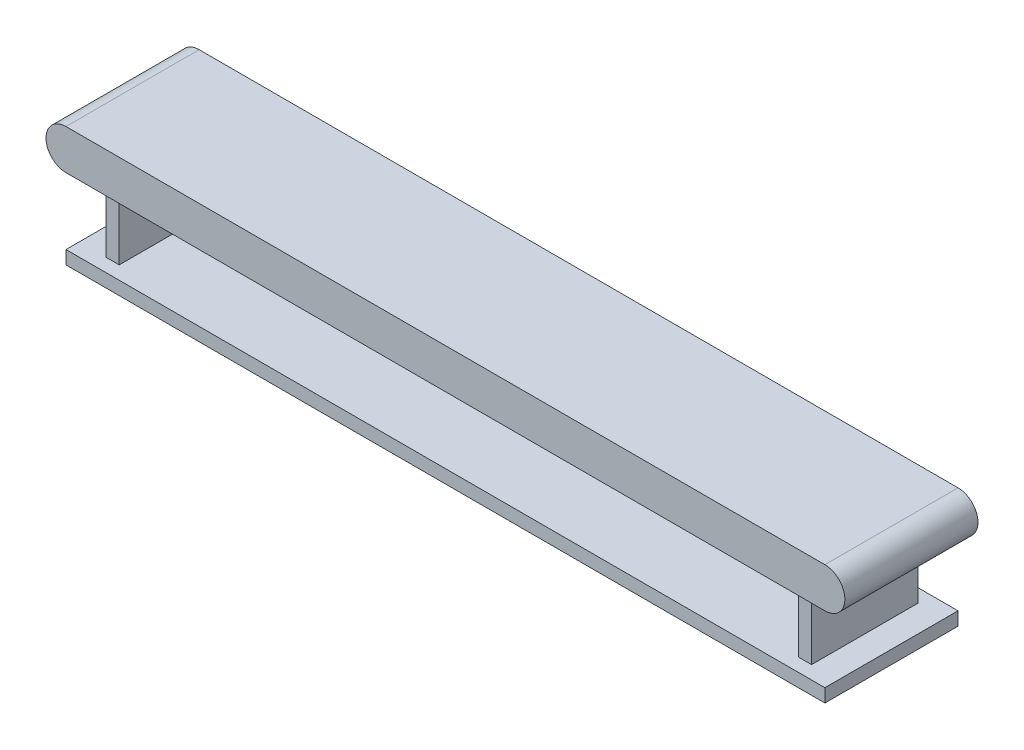
SolidWorks part; units mm, degrees
ref_plane "Front Plane" through (0, 0, 0) normal (0, 0, 1) x (1, 0, 0)
ref_plane "Top Plane" through (0, 0, 0) normal (0, 1, 0) x (1, 0, 0)
ref_plane "Right Plane" through (0, 0, 0) normal (1, 0, 0) x (0, 0, -1)
sketch "Sketch1" plane through (0, 0, 0) normal (0, 1, 0) x (1, 0, 0)
  line L1 (-3000, -500) -> (3000, -500)
  line L2 (-3000, -500) -> (-3000, 500)
  line L3 (-3000, 500) -> (3000, 500)
  line L4 (3000, -500) -> (3000, 500)
  line L5 (0, 500) -> (0, -500) construction
  line L6 (-3000, 0) -> (3000, 0) construction
  point P0 (0, 0)
  dimension "D1" = 6000
  dimension "D2" = 1000
extrude "Boss-Extrude1" add sketch "Sketch1" along normal blind 300
sketch "Sketch4" plane through (0, 0, 500) normal (0, 0, 1) x (1, 0, 0)
  line L0 (-3000, 300) -> (-3000, 0) construction
  line L1 (-3000, 300) -> (3000, 300) construction
  line L2 (-3000, 0) -> (3000, 0) construction
  line L3 (-3000, 300) -> (-2850, 300)
  line L4 (-3000, 300) -> (-3000, 0)
  line L5 (-3000, 0) -> (-2850, 0)
  line L6 (3000, 300) -> (3000, 0) construction
  line L7 (3000, 300) -> (3000, 0)
  line L8 (2850, 0) -> (3000, 0)
  line L9 (2850, 300) -> (3000, 300)
  arc A0 (-2850, 300) -> (-2850, 0) centre (-2850, 150) ccw
  arc A1 (2850, 0) -> (2850, 300) centre (2850, 150) ccw
  line M2 (-3000, 0) -> (3000, 0)
  line M3 (3000, 0) -> (3000, 300)
  line M4 (3000, 300) -> (-3000, 300)
  line M5 (-3000, 300) -> (-3000, 0)
  dimension "D1" = 150
  dimension "D2" = 150
extrude "Cut-Extrude1" cut sketch "Sketch4" against normal through all contours A1 L7 M4 | A1 M2 M3 | A0 M4 M5 | A0 L4 M2
sketch "Sketch5" plane through (0, 0, 0) normal (0, -1, 0) x (-1, 0, 0)
  line L0 (-2850, 500) -> (2850, 500) construction
  line L1 (2650, 400) -> (2550, 400)
  line L2 (2650, 400) -> (2650, -400)
  line L3 (2650, -400) -> (2550, -400)
  line L4 (2550, 400) -> (2550, -400)
  line L5 (2600, -400) -> (2600, 400) construction
  line L6 (2650, 0) -> (2550, 0) construction
  line L7 (2850, 500) -> (2850, -500) construction
  line L8 (0, 165) -> (0, -165) construction
  line L9 (-2650, 400) -> (-2550, 400)
  line L10 (-2650, 400) -> (-2650, -400)
  line L11 (-2550, 400) -> (-2550, -400)
  line L12 (-2650, -400) -> (-2550, -400)
  point P0 (2600, 0)
  dimension "D1" = 100
  dimension "D2" = 800
  dimension "D3" = 100
  dimension "D4" = 200
extrude "Boss-Extrude2" add sketch "Sketch5" along normal blind 500 contours L2 L1 L4 L3 | L9 L11 L12 L10
ref_plane "Plane1" through (0, -500, 0) normal (0, -1, 0) x (-1, 0, 0)
sketch "Sketch6" plane through (0, -500, 0) normal (0, -1, 0) x (-1, 0, 0)
  line L1 (-2850, 500) -> (2850, 500)
  line L2 (-2850, 500) -> (-2850, -500)
  line L3 (-2850, -500) -> (2850, -500)
  line L4 (2850, 500) -> (2850, -500)
  line L5 (0, -500) -> (0, 500) construction
  line L6 (-2850, 0) -> (2850, 0) construction
  point P0 (0, 0)
  dimension "D1" = 1000
  dimension "D2" = 5700
extrude "Boss-Extrude3" add sketch "Sketch6" along normal blind 100
